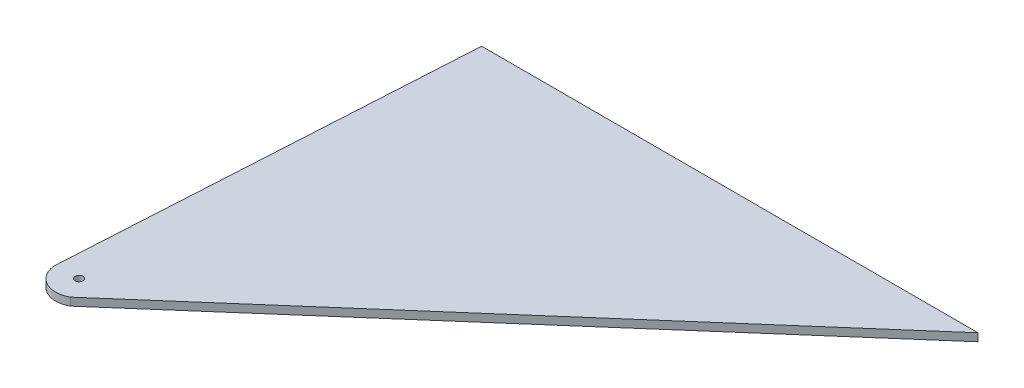
SolidWorks part; units mm, degrees
ref_plane "Plan de face" through (0, 0, 0) normal (0, 0, 1) x (1, 0, 0)
ref_plane "Plan de dessus" through (0, 0, 0) normal (0, 1, 0) x (1, 0, 0)
ref_plane "Plan de droite" through (0, 0, 0) normal (1, 0, 0) x (0, 0, -1)
sketch "Esquisse1" plane through (0, 0, 0) normal (0, 1, 0) x (1, 0, 0)
  line L0 (0, 0) -> (0, 103) construction
  line L6 (0, 103) -> (127, 103)
  line L7 (0, 103) -> (-6, 0)
  line L8 (127, 103) -> (3, -5.1962)
  circle A0 centre (0, 0) radius 1
  arc A1 (3, -5.1962) -> (-6, 0) centre (0, 0) cw
  point P6 (-6, 0)
  dimension "D2" = 2
  dimension "D3" = 6
  dimension "D4" = 127
  dimension "D1" = 103
  dimension "D5" = 3.334
  dimension "D6" = 120
extrude "Boss.-Extru.2" add sketch "Esquisse1" along normal blind 2
